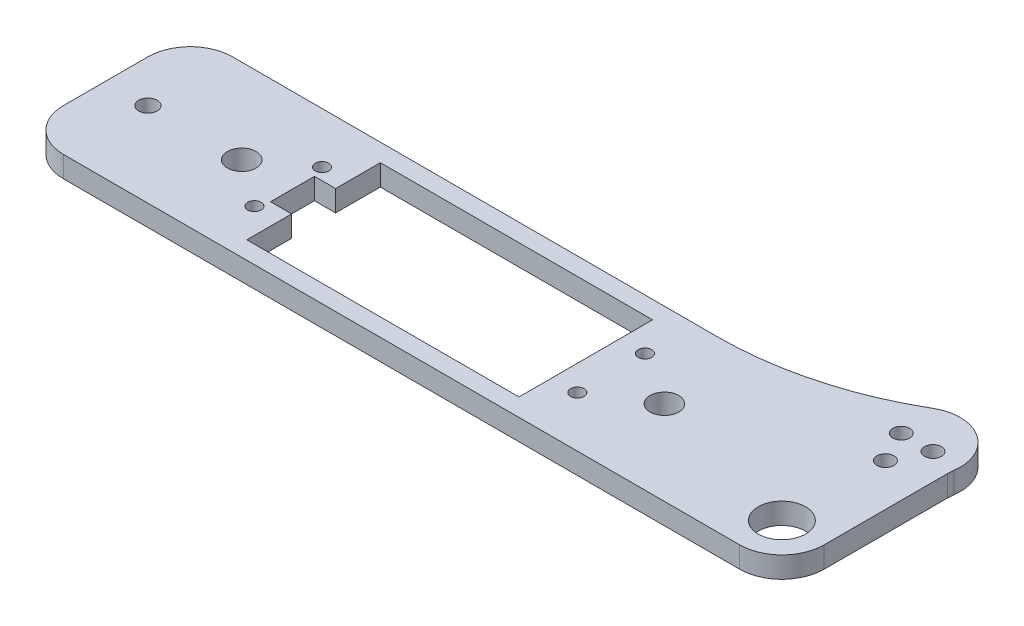
SolidWorks part; units mm, degrees
ref_plane "Front Plane" through (0, 0, 0) normal (0, 0, 1) x (1, 0, 0)
ref_plane "Top Plane" through (0, 0, 0) normal (0, 1, 0) x (1, 0, 0)
ref_plane "Right Plane" through (0, 0, 0) normal (1, 0, 0) x (0, 0, -1)
ref_plane "Plane1" through (0, -3.175, 0) normal (0, -1, 0) x (1, 0, 0)
sketch "Sketch1" plane through (0, -3.175, 0) normal (0, -1, 0) x (1, 0, 0)
  line L0 (-25.908, 10.033) -> (14.986, 10.033)
  line L1 (14.986, 10.033) -> (14.986, -10.033)
  line L2 (14.986, -10.033) -> (-25.908, -10.033)
  line L3 (-25.908, -10.033) -> (-25.908, -3.302)
  line L4 (-25.908, -3.302) -> (-29.083, -3.302)
  line L5 (-29.083, -3.302) -> (-29.083, 3.302)
  line L6 (-29.083, 3.302) -> (-25.908, 3.302)
  line L7 (-25.908, 3.302) -> (-25.908, 10.033)
  line L8 (57.15, -12.1784) -> (57.15, 6.35)
  line L9 (50.8, 12.7) -> (-50.8, 12.7)
  line L10 (-57.15, 6.35) -> (-57.15, -6.35)
  line L11 (-50.8, -12.7) -> (22.0373, -12.7)
  circle A0 centre (26.797, 0) radius 2.159
  circle A1 centre (-36.703, 0) radius 2.159
  circle A2 centre (-29.718, -5.08) radius 1.016
  circle A3 centre (18.796, -5.08) radius 1.016
  circle A4 centre (18.796, 5.08) radius 1.016
  circle A5 centre (-29.718, 5.08) radius 1.016
  circle A6 centre (50.8, -9.2075) radius 1.27
  circle A7 centre (48.4188, -13.97) radius 1.27
  circle A8 centre (53.1812, -13.97) radius 1.27
  circle A9 centre (50.8, 6.35) radius 3.556
  circle A10 centre (-50.8, 0) radius 1.397
  arc A11 (57.15, 6.35) -> (50.8, 12.7) centre (50.8, 6.35) ccw
  arc A12 (-50.8, 12.7) -> (-57.15, 6.35) centre (-50.8, 6.35) ccw
  arc A13 (-57.15, -6.35) -> (-50.8, -12.7) centre (-50.8, -6.35) ccw
  arc A14 (22.0373, -12.7) -> (47.548, -19.57) centre (22.0373, -63.5) cw
  arc A15 (47.548, -19.57) -> (57.2123, -13.0654) centre (50.8, -13.97) ccw
  arc A16 (57.2123, -13.0654) -> (57.15, -12.1784) centre (63.5, -12.1784) cw
extrude "Boss-Extrude1" add sketch "Sketch1" against normal blind 3.175
